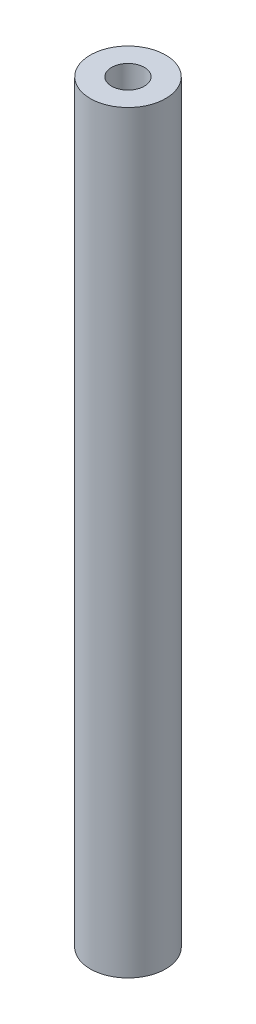
SolidWorks part; units mm, degrees
material "1060 合金"
ref_plane "前视基准面" through (0, 0, 0) normal (0, 0, 1) x (1, 0, 0)
ref_plane "上视基准面" through (0, 0, 0) normal (0, 1, 0) x (1, 0, 0)
ref_plane "右视基准面" through (0, 0, 0) normal (1, 0, 0) x (0, 0, -1)
other "Configuration Table"
sketch "草图1" plane through (0, 0, 0) normal (0, 1, 0) x (1, 0, 0)
  circle A0 centre (0, 0) radius 1.52
  circle A1 centre (0, 0) radius 3.5
extrude "凸台-拉伸1" add sketch "草图1" along normal blind 70
